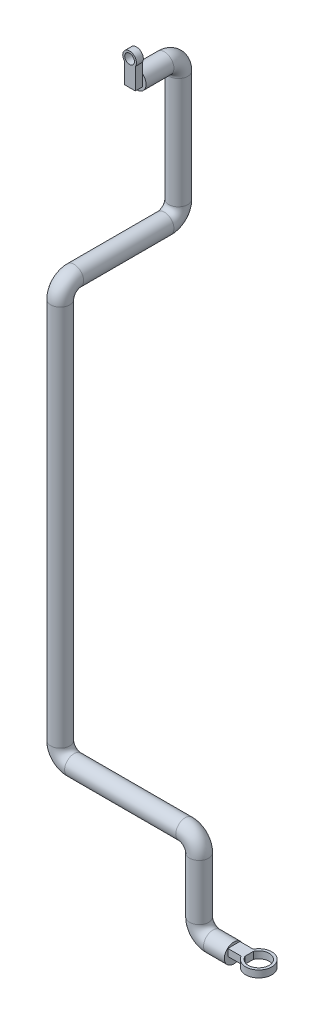
SolidWorks part; units mm, degrees
ref_plane "Alzado" through (0, 0, 0) normal (0, 0, 1) x (1, 0, 0)
ref_plane "Planta" through (0, 0, 0) normal (0, 1, 0) x (1, 0, 0)
ref_plane "Vista lateral" through (0, 0, 0) normal (1, 0, 0) x (0, 0, -1)
sketch3d "Croquis3D1"
  line L0 (0, 0, 0) -> (-30, 0, 0)
  line L1 (-50, 20, 0) -> (-50, 100, 0)
  line L5 (-70, 120, 0) -> (-230, 120, 0)
  line L6 (-250, 140, 0) -> (-250, 690, 0)
  line L7 (-250, 710, -20) -> (-250, 710, -150)
  line L8 (-250, 730, -170) -> (-250, 890, -170)
  line L9 (-250, 910, -150) -> (-250, 910, -109.8474)
  arc A0 (-250, 890, -170) -> (-250, 910, -150) centre (-250, 890, -150) ccw
  arc A1 (-250, 710, -150) -> (-250, 730, -170) centre (-250, 730, -150) ccw
  arc A2 (-250, 690, 0) -> (-250, 710, -20) centre (-250, 690, -20) ccw
  arc A3 (-230, 120, 0) -> (-250, 140, 0) centre (-230, 140, 0) ccw
  arc A4 (-30, 0, 0) -> (-50, 20, 0) centre (-30, 20, 0) ccw
  arc A5 (-70, 120, 0) -> (-50, 100, 0) centre (-70, 100, 0) ccw
  point P5 (-250, 910, -170)
  point P11 (-230, 890, -150)
  point P15 (-250, 710, -170)
  point P16 (-230, 730, -150)
  point P19 (-250, 710, 0)
  point P20 (-270, 690, -20)
  point P23 (-250, 120, 0)
  point P24 (-230, 140, -20)
  point P27 (-50, 0, 0)
  point P28 (-30, 20, -20)
  point P31 (-50, 120, 0)
  point P32 (-70, 100, -20)
  dimension "D6" = 20
  dimension "D1" = 50
  dimension "D2" = 120
  dimension "D4" = 590
  dimension "D3" = 200
  dimension "D5" = 200
  dimension "D7" = 170
sketch "Croquis1" plane through (0, 0, 0) normal (1, 0, 0) x (0, 0, -1)
  circle A0 centre (0, 0) radius 13.7
  dimension "D1" = 27.4
sweep "Barrer1" add profiles "Croquis1" path "Croquis3D1"
ref_plane "Plano1" through (0, 0, 0) normal (1, 0, 0) x (0, 0, -1)
sketch "Croquis2" plane through (0, 0, 0) normal (0, 1, 0) x (1, 0, 0)
  circle A0 centre (35.8291, 0) radius 18.8024
  circle A1 centre (35.8291, 0) radius 15
  dimension "D1" = 30
extrude "Saliente-Extruir1" add sketch "Croquis2" along normal blind 10 separate body
sketch "Croquis3" plane through (0, 0, 0) normal (0, 1, 0) x (1, 0, 0)
  line L0 (17.0268, 0) -> (-30, 0) construction
  line L1 (-30, 13.7) -> (-30, -13.7) construction
  line L3 (-22.0679, 8.6555) -> (22.0679, 8.6555)
  line L4 (-22.0679, 8.6555) -> (-22.0679, -8.6555)
  line L5 (-22.0679, -8.6555) -> (22.0679, -8.6555)
  line L6 (22.0679, 8.6555) -> (22.0679, -8.6555)
  line L7 (-22.0679, 8.6555) -> (22.0679, -8.6555) construction
  line L8 (-22.0679, -8.6555) -> (22.0679, 8.6555) construction
  circle A0 centre (35.8291, 0) radius 18.8024 construction
  point P6 (0, 0)
extrude "Saliente-Extruir2" add sketch "Croquis3" along normal blind 10
sketch "Croquis4" plane through (0, 0, -109.8474) normal (0, 0, 1) x (1, 0, 0)
  line L0 (-250, 910) -> (-250, 940) construction
  circle A0 centre (-250, 940) radius 7
  circle A1 centre (-250, 940) radius 9.8566
  dimension "D1" = 14
  dimension "D2" = 30
extrude "Saliente-Extruir3" add sketch "Croquis4" along normal blind 10 separate body
sketch "Croquis5" plane through (0, 0, -109.8474) normal (0, 0, 1) x (1, 0, 0)
  line L0 (-245.5319, 934.6114) -> (-241.7467, 934.6114)
  line L1 (-256.9563, 912.7578) -> (-241.7467, 912.7578)
  line L2 (-256.9563, 912.7578) -> (-256.9563, 934.6114)
  line L3 (-256.9563, 934.6114) -> (-254.4681, 934.6114)
  line L4 (-241.7467, 912.7578) -> (-241.7467, 934.6114)
  line L5 (-256.9563, 912.7578) -> (-241.7467, 934.6114) construction
  line L6 (-256.9563, 934.6114) -> (-241.7467, 912.7578) construction
  circle A0 centre (-250, 910) radius 13.7 construction
  circle A1 centre (-250, 940) radius 9.8566 construction
  circle A2 centre (-250, 940) radius 7
  point P0 (-249.3515, 923.6846)
  circle M1 centre (-250, 910) radius 13.7
extrude "Saliente-Extruir4" add sketch "Croquis5" along normal blind 10 contours A2 L3 L2 L4 L0 M1
sketch "Croquis6" plane through (0, 0, -99.8474) normal (0, 0, 1) x (1, 0, 0)
  line L0 (-256.9563, 921.8026) -> (-256.9563, 904.0487)
  line L1 (-256.9563, 904.0487) -> (-241.7467, 904.0487)
  line L2 (-241.7467, 904.0487) -> (-241.7467, 920.935)
  arc A0 (-241.7467, 920.935) -> (-256.9563, 921.8026) centre (-250, 910) ccw
extrude "Saliente-Extruir5" add sketch "Croquis6" against normal blind 10
